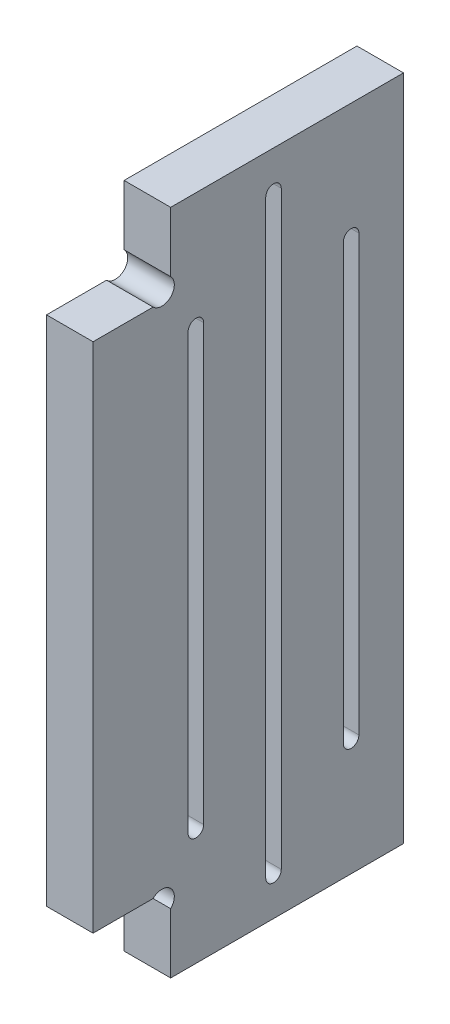
SolidWorks part; units mm, degrees
ref_plane "Plan de face" through (0, 0, 0) normal (0, 0, 1) x (1, 0, 0)
ref_plane "Plan de dessus" through (0, 0, 0) normal (0, 1, 0) x (1, 0, 0)
ref_plane "Plan de droite" through (0, 0, 0) normal (1, 0, 0) x (0, 0, -1)
sketch "Esquisse1" plane through (0, 0, 0) normal (1, 0, 0) x (0, 0, -1)
  line L4 (110, 226.8628) -> (80, 226.8628)
  line L6 (77.7373, 150.8628) -> (70, 150.8628)
  line L8 (77.7373, 216.8628) -> (70, 216.8628)
  line L9 (80, 140.8628) -> (80, 148.6001)
  line L12 (70, 150.8628) -> (70, 216.8628)
  line L13 (80, 219.1256) -> (80, 226.8628)
  line L46 (80, 140.8628) -> (110, 140.8628)
  line L49 (110, 140.8628) -> (110, 226.8628)
  arc A0 (80, 148.6001) -> (77.7373, 150.8628) centre (78.8686, 149.7315) ccw
  arc A1 (80, 219.1256) -> (77.7373, 216.8628) centre (78.8686, 217.9942) cw
  dimension "D4" = 10
  dimension "D12" = 30
  dimension "D7" = 8.8686
  dimension "D9" = 86
  dimension "D11" = 1.6
  dimension "D2" = 1.6
  dimension "D3" = 10
  dimension "D5" = 10
  dimension "D6" = 8.8686
  dimension "D8" = 8.8686
  dimension "D10" = 10
extrude "Extrusion1" add sketch "Esquisse1" along normal blind 6
sketch "Esquisse3" plane through (0, 0, 0) normal (-1, 0, 0) x (0, 0, 1)
  line L0 (-83.25, 155.8628) -> (-83.25, 211.8628) construction
  line L1 (-84.25, 155.8628) -> (-84.25, 211.8628)
  line L2 (-82.25, 155.8628) -> (-82.25, 211.8628)
  line L3 (-93.25, 145.8628) -> (-93.25, 221.8628) construction
  line L4 (-94.25, 145.8628) -> (-94.25, 221.8628)
  line L5 (-92.25, 145.8628) -> (-92.25, 221.8628)
  line L6 (-103.25, 155.8628) -> (-103.25, 211.8628) construction
  line L7 (-104.25, 155.8628) -> (-104.25, 211.8628)
  line L8 (-102.25, 155.8628) -> (-102.25, 211.8628)
  line L9 (-80, 140.8628) -> (-110, 140.8628) construction
  line L10 (-110, 226.8628) -> (-80, 226.8628) construction
  line L11 (-80, 148.6001) -> (-80, 140.8628) construction
  arc A0 (-84.25, 155.8628) -> (-82.25, 155.8628) centre (-83.25, 155.8628) ccw
  arc A1 (-82.25, 211.8628) -> (-84.25, 211.8628) centre (-83.25, 211.8628) ccw
  arc A2 (-94.25, 145.8628) -> (-92.25, 145.8628) centre (-93.25, 145.8628) ccw
  arc A3 (-92.25, 221.8628) -> (-94.25, 221.8628) centre (-93.25, 221.8628) ccw
  arc A4 (-104.25, 155.8628) -> (-102.25, 155.8628) centre (-103.25, 155.8628) ccw
  arc A5 (-102.25, 211.8628) -> (-104.25, 211.8628) centre (-103.25, 211.8628) ccw
  point P2 (-83.25, 183.8628)
  point P7 (-93.25, 183.8628)
  point P14 (-103.25, 183.8628)
  point P25 (0, 0)
  point P26 (0, 0)
  point P29 (0, 0)
  point P30 (0, 0)
  point P31 (0, 0)
  point P32 (0, 0)
  dimension "D1" = 1
  dimension "D2" = 1
  dimension "D3" = 1
  dimension "D4" = 15
  dimension "D5" = 15
  dimension "D6" = 3.25
  dimension "D7" = 10
  dimension "D8" = 10
  dimension "D9" = 5
  dimension "D10" = 5
extrude "Enlèv. mat.-Extru.2" cut sketch "Esquisse3" against normal through all
